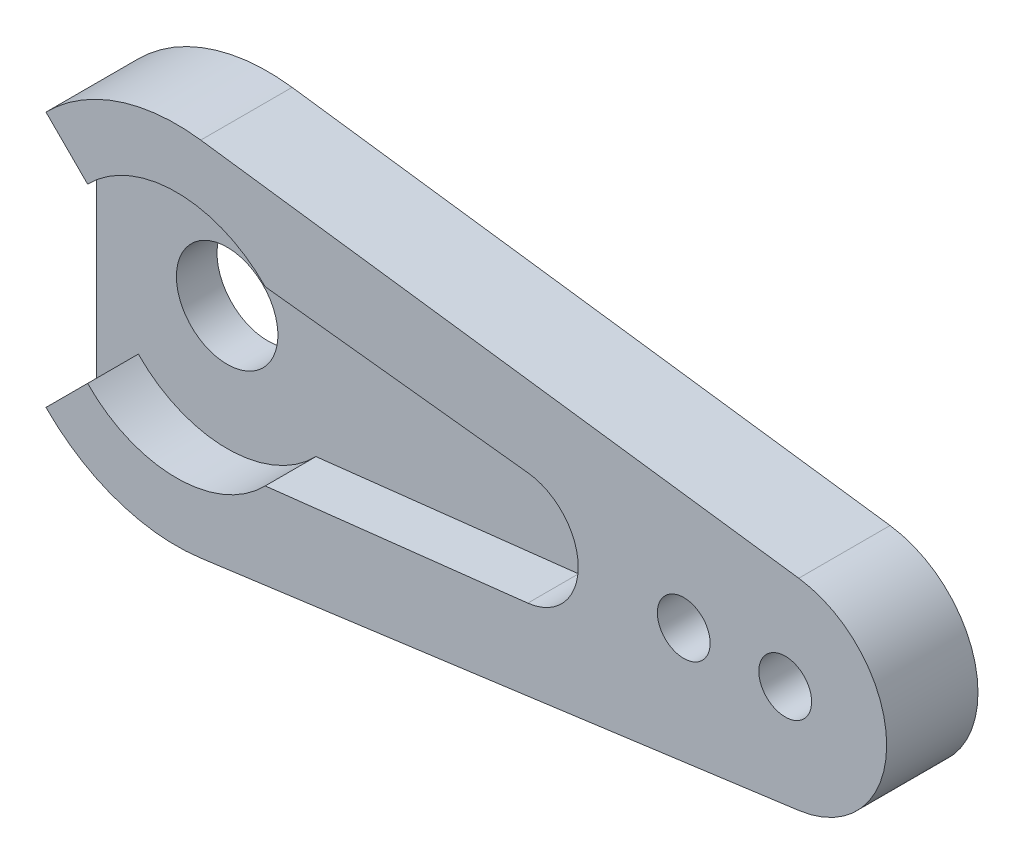
SolidWorks part; units mm, degrees
ref_plane "Front Plane" through (0, 0, 0) normal (0, 0, 1) x (1, 0, 0)
ref_plane "Top Plane" through (0, 0, 0) normal (0, 1, 0) x (1, 0, 0)
ref_plane "Right Plane" through (0, 0, 0) normal (1, 0, 0) x (0, 0, -1)
sketch "Esquisse1" plane through (0, 0, 0) normal (0, 0, 1) x (1, 0, 0)
  line L0 (-4.3758, 4.25) -> (-6.4265, 6.3008)
  line L1 (4.3758, 4.25) -> (17.3156, 2.7822)
  line L2 (17.3156, -2.7822) -> (4.3758, -4.25)
  line L4 (1.2, 8.9196) -> (30.6667, 4.9554)
  line L5 (1.2, -8.9196) -> (30.6667, -4.9554)
  line L6 (-4.3758, -4.25) -> (-6.4265, -6.3008)
  arc A0 (4.3758, 4.25) -> (-4.3758, 4.25) centre (0, 0) ccw
  arc A1 (17.3156, -2.7822) -> (17.3156, 2.7822) centre (17, 0) ccw
  arc A2 (4.3758, -4.25) -> (-4.3758, -4.25) centre (0, 0) cw
  arc A3 (-6.4265, 6.3008) -> (1.2, 8.9196) centre (0, 0) cw
  arc A4 (30.6667, 4.9554) -> (30.6667, -4.9554) centre (30, 0) cw
  arc A5 (-6.4265, -6.3008) -> (1.2, -8.9196) centre (0, 0) ccw
  dimension "D2" = 6.1
  dimension "D3" = 2.8
  dimension "D5" = 36.4265
  dimension "D6" = 9
  dimension "D8" = 5
  dimension "D1" = 8.5
  dimension "D4" = 17
  dimension "D7" = 30
extrude "Main" add sketch "Esquisse1" along normal blind 2.5
sketch "Esquisse2" plane through (0, 0, 0) normal (0, 0, -1) x (-1, 0, 0)
  line L0 (-1.2, -8.9196) -> (-30.6667, -4.9554)
  line L1 (-1.2, -8.9196) -> (-30.6667, -4.9554) construction
  line L3 (-1.2, 8.9196) -> (-30.6667, 4.9554)
  line L4 (6.4265, -6.3008) -> (6.4265, 6.3008)
  arc A0 (-30.6667, 4.9554) -> (-30.6667, -4.9554) centre (-30, 0) ccw construction
  arc A1 (-1.2, -8.9196) -> (6.4265, -6.3008) centre (0, 0) ccw
  circle A2 centre (0, 0) radius 2.5
  arc A3 (6.4265, 6.3008) -> (-1.2, 8.9196) centre (0, 0) ccw
  arc A5 (-30.6667, 4.9554) -> (-30.6667, -4.9554) centre (-30, 0) ccw
  arc A6 (-1.2, -8.9196) -> (6.4265, -6.3008) centre (0, 0) ccw construction
  dimension "D1" = 5
extrude "OriginalBracket" add sketch "Esquisse2" along normal blind 2
sketch "Esquisse3" plane through (0, 0, 2.5) normal (0, 0, 1) x (1, 0, 0)
  circle A0 centre (30, 0) radius 1.3
  arc A2 (30.6667, -4.9554) -> (30.6667, 4.9554) centre (30, 0) ccw construction
  circle A3 centre (25, 0) radius 1.3
  dimension "D1" = 2.6
  dimension "D2" = 5
extrude "FixingHole" cut sketch "Esquisse3" against normal through all
